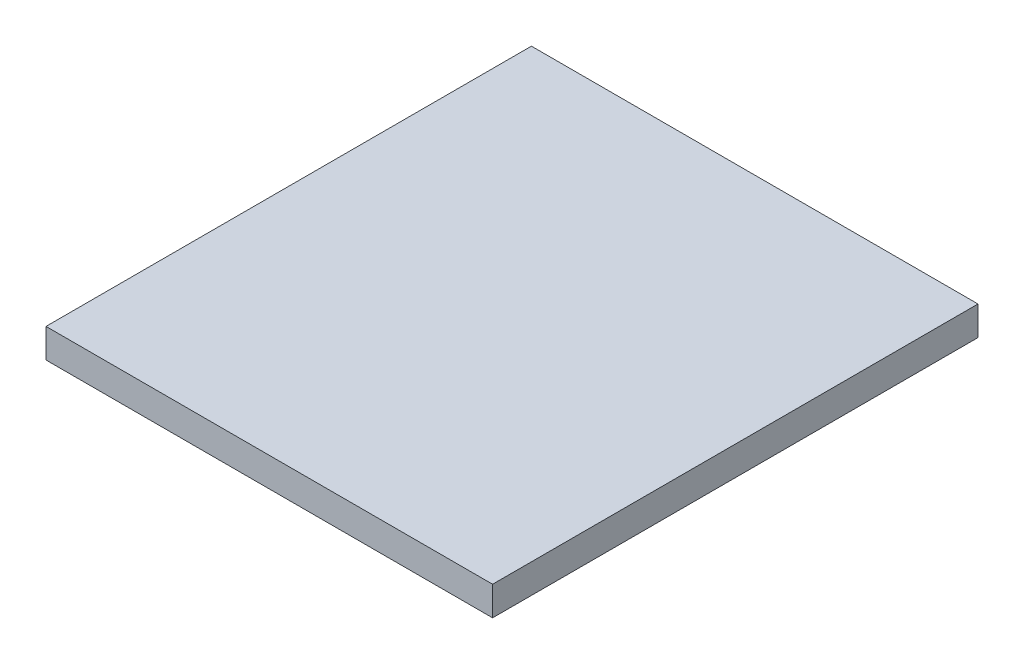
SolidWorks part; units mm, degrees
material "Mahogany"
ref_plane "Front Plane" through (0, 0, 0) normal (0, 0, 1) x (1, 0, 0)
ref_plane "Top Plane" through (0, 0, 0) normal (0, 1, 0) x (1, 0, 0)
ref_plane "Right Plane" through (0, 0, 0) normal (1, 0, 0) x (0, 0, -1)
sketch "Sketch1" plane through (0, 0, 0) normal (0, 1, 0) x (1, 0, 0)
  line L1 (-23, 25) -> (23, 25)
  line L2 (-23, 25) -> (-23, -25)
  line L3 (-23, -25) -> (23, -25)
  line L4 (23, 25) -> (23, -25)
  line L5 (-23, 25) -> (23, -25) construction
  line L6 (-23, -25) -> (23, 25) construction
  point P0 (0, 0)
  dimension "D1" = 46
  dimension "D2" = 50
extrude "Boss-Extrude1" add sketch "Sketch1" along normal blind 3
